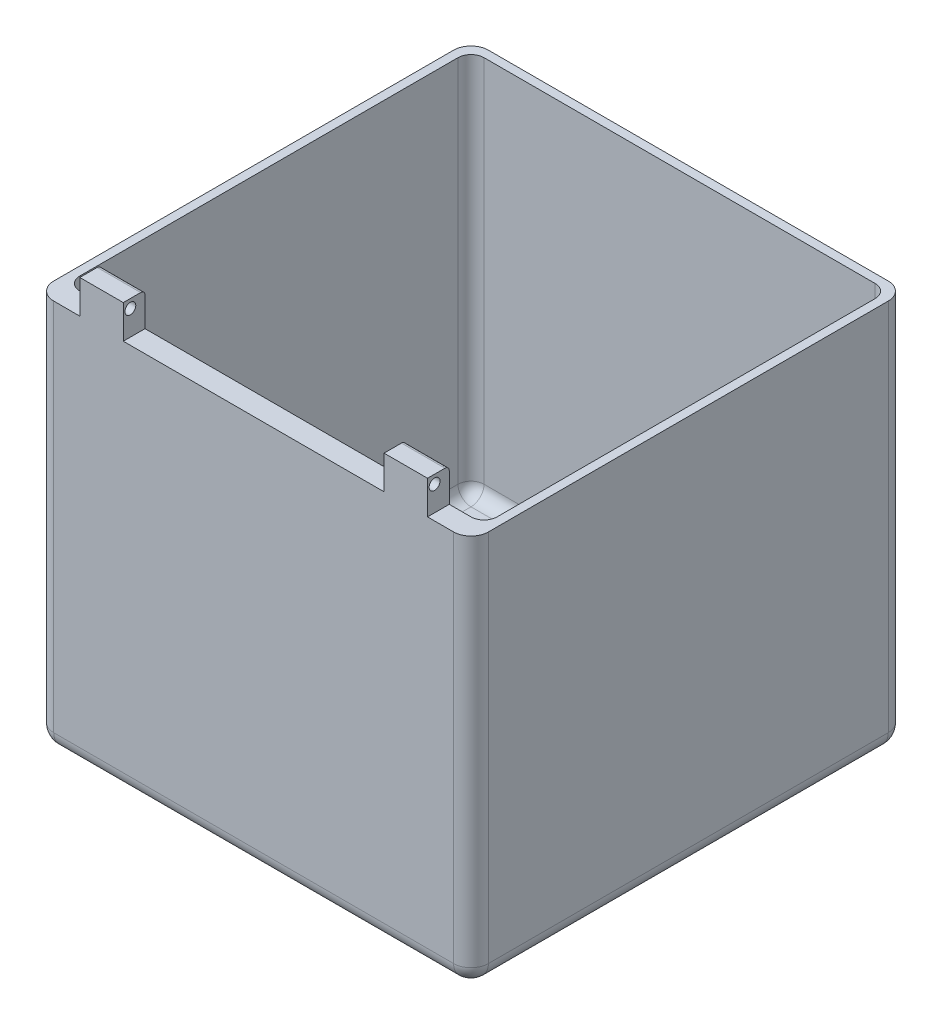
SolidWorks part; units mm, degrees
ref_plane "Front Plane" through (0, 0, 0) normal (0, 0, 1) x (1, 0, 0)
ref_plane "Top Plane" through (0, 0, 0) normal (0, 1, 0) x (1, 0, 0)
ref_plane "Right Plane" through (0, 0, 0) normal (1, 0, 0) x (0, 0, -1)
sketch "Sketch1" plane through (0, 0, 0) normal (0, 1, 0) x (1, 0, 0)
  line L1 (-50, -50) -> (50, -50)
  line L2 (-50, -50) -> (-50, 50)
  line L3 (-50, 50) -> (50, 50)
  line L4 (50, -50) -> (50, 50)
  line L5 (-50, -50) -> (50, 50) construction
  line L6 (-50, 50) -> (50, -50) construction
  point P0 (0, 0)
  dimension "D1" = 100
extrude "Boss-Extrude1" add sketch "Sketch1" along normal blind 90
sketch "Sketch2" plane through (0, 90, 0) normal (0, 1, 0) x (1, 0, 0)
  line L0 (48, -45) -> (48, 48)
  line L1 (48, 48) -> (-48, 48)
  line L2 (-48, 48) -> (-48, -45)
  line L4 (50, -50) -> (50, 50)
  line L5 (50, 50) -> (-50, 50)
  line L6 (-50, 50) -> (-50, -50)
  line L7 (-50, -50) -> (50, -50)
  line L8 (50, -50) -> (50, 50) construction
  line L9 (50, 50) -> (-50, 50) construction
  line L10 (-50, 50) -> (-50, -50) construction
  line L11 (-50, -50) -> (50, -50) construction
  line L12 (-48, -45) -> (48, -45)
  line L13 (-48, 48) -> (-48, -48) construction
  line L14 (48, -48) -> (48, 48) construction
  line L16 (-48, -48) -> (48, -48) construction
  dimension "D3" = 5
  dimension "D1" = 0
  dimension "D2" = 2
extrude "Cut-Extrude1" cut sketch "Sketch2" against normal offset from surface (88 mm away) 2 up to face at (0, 0, 0)
sketch "Sketch3" plane through (0, 2, 0) normal (0, 1, 0) x (1, 0, 0)
  line L0 (-48, 0) -> (48, 0) construction
  line L3 (0, 0) -> (22, 0) construction
  line L4 (0, 1.25) -> (22, 1.25)
  line L5 (0, -1.25) -> (22, -1.25)
  line L6 (0, 0) -> (0, 33.2004) construction
  line L7 (-30, 20) -> (30, 20) construction
  line L8 (-30, 20) -> (-30, -20) construction
  line L9 (-30, -20) -> (30, -20) construction
  line L10 (30, 20) -> (30, -20) construction
  line L11 (-30, 20) -> (30, -20) construction
  line L12 (-30, -20) -> (30, 20) construction
  arc A0 (0, 1.25) -> (0, -1.25) centre (0, 0) ccw
  arc A1 (22, -1.25) -> (22, 1.25) centre (22, 0) ccw
  circle A2 centre (-14.25, 0) radius 3
  circle A3 centre (-30, 20) radius 1.75
  circle A4 centre (-30, -20) radius 1.75
  circle A5 centre (30, -20) radius 1.75
  circle A6 centre (30, 20) radius 1.75
  point P3 (11, 0)
  point P16 (0, 0)
  dimension "D2" = 22
  dimension "D3" = 6
  dimension "D4" = 10
  dimension "D5" = 8
  dimension "D7" = 3.5
  dimension "D1" = 2.5
  dimension "D6" = 20
extrude "Cut-Extrude2" cut sketch "Sketch3" against normal up to next
chamfer "Chamfer1" distance 0.8 angle 45 4 edges at (30, 0, 18.25) (-30, 0, 18.25) (-30, 0, -21.75) (30, 0, -21.75)
sketch "Sketch4" plane through (0, 90, 0) normal (0, 1, 0) x (1, 0, 0)
  line L2 (-48, -45) -> (48, -45) construction
  line L3 (-50, -50) -> (50, -50) construction
  line L4 (0, 0) -> (0, -59.746) construction
  line L5 (-40, -45) -> (-30, -45)
  line L6 (-48, -45) -> (48, -45) construction
  line L7 (-50, -50) -> (50, -50) construction
  line L8 (-40, -45) -> (-40, -50)
  line L9 (-40, -50) -> (-30, -50)
  line L10 (-30, -45) -> (-30, -50)
  line L11 (30, -45) -> (30, -50)
  line L12 (40, -50) -> (30, -50)
  line L13 (40, -45) -> (40, -50)
  line L14 (40, -45) -> (30, -45)
  dimension "D1" = 10
  dimension "D2" = 10
extrude "Boss-Extrude2" add sketch "Sketch4" along normal blind 7.7
sketch "Sketch5" plane through (-40, 0, 0) normal (-1, 0, 0) x (0, 0, 1)
  line L4 (45, 90) -> (50, 90)
  line L5 (50, 90) -> (50, 97.7)
  line L6 (50, 97.7) -> (45, 97.7)
  line L7 (45, 97.7) -> (45, 90)
  line L8 (45, 90) -> (50, 90) construction
  line L9 (50, 90) -> (50, 97.7) construction
  line L10 (50, 97.7) -> (45, 97.7) construction
  line L11 (45, 97.7) -> (45, 90) construction
  circle A0 centre (48.375, 95.7) radius 1.25
  dimension "D2" = 2.5
  dimension "D3" = 0.375
  dimension "D4" = 0.75
  dimension "D1" = 0
extrude "Cut-Extrude3" cut sketch "Sketch5" against normal through all
fillet "Fillet1" radius 3 8 edges at (48, 46, 45) (48, 46, -48) (-48, 46, 45) (0, 2, 45) (48, 2, -1.5) (-48, 46, -48) (0, 2, -48) (-48, 2, -1.5)
fillet "Fillet2" radius 4 8 edges at (0, 0, 50) (-50, 0, 0) (0, 0, -50) (50, 0, 0) (50, 45, -50) (50, 45, 50) (-50, 45, 50) (-50, 45, -50)
fillet "Fillet3" radius 1 2 edges at (35, 97.7, 45) (-35, 97.7, 45)
